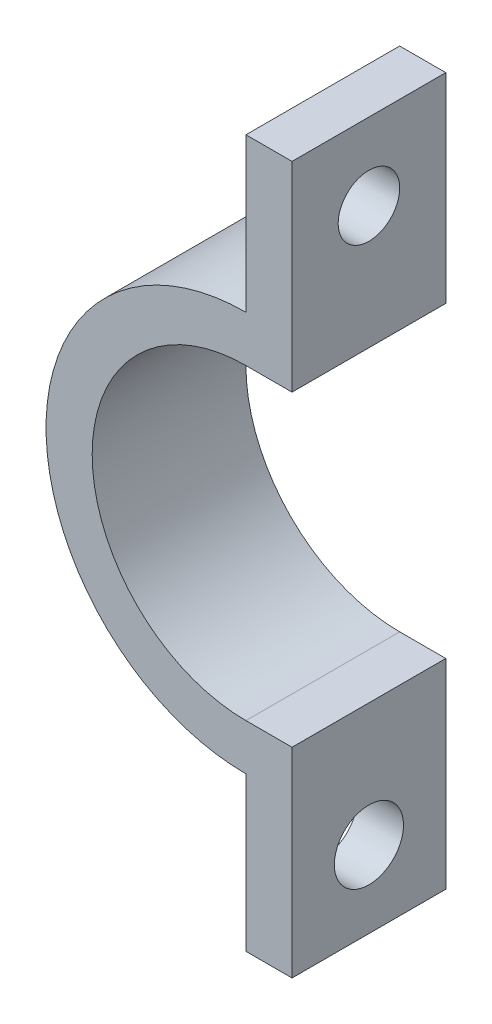
SolidWorks part; units mm, degrees
ref_plane "前视基准面" through (0, 0, 0) normal (0, 0, 1) x (1, 0, 0)
ref_plane "上视基准面" through (0, 0, 0) normal (0, 1, 0) x (1, 0, 0)
ref_plane "右视基准面" through (0, 0, 0) normal (1, 0, 0) x (0, 0, -1)
sketch "草图1" plane through (0, 0, 0) normal (0, 0, 1) x (1, 0, 0)
  line L2 (0, 23) -> (3, 23)
  line L3 (3, 23) -> (3, 10)
  line L4 (3, 10) -> (0, 10)
  line L5 (0, 0) -> (26.4825, 0) construction
  line L6 (0, -23) -> (3, -23)
  line L8 (3, -23) -> (3, -10)
  line L9 (3, -10) -> (0, -10)
  line L11 (0, 13) -> (0, 23)
  line L12 (0, -13) -> (0, -23)
  arc A0 (0, 10) -> (0, -10) centre (0, 0) ccw
  arc A1 (0, 13) -> (0, -13) centre (0, 0) ccw
  dimension "D1" = 10
  dimension "D2" = 13
  dimension "D5" = 23
  dimension "D3" = 13
  dimension "D4" = 3
extrude "凸台-拉伸1" add sketch "草图1" along normal blind 10
sketch "草图3" plane through (0, 0, 0) normal (-1, 0, 0) x (0, 0, 1)
  line L0 (0, 13) -> (10, 23) construction
  circle A0 centre (5, 18) radius 2
extrude "切除-拉伸2" cut sketch "草图3" against normal through all
sketch "草图4" plane through (0, 0, 0) normal (-1, 0, 0) x (0, 0, 1)
  line L0 (0, -23) -> (10, -13) construction
  circle A0 centre (5, -18) radius 2.25
  dimension "D1" = 4.5
extrude "切除-拉伸3" cut sketch "草图4" against normal blind 3.2
